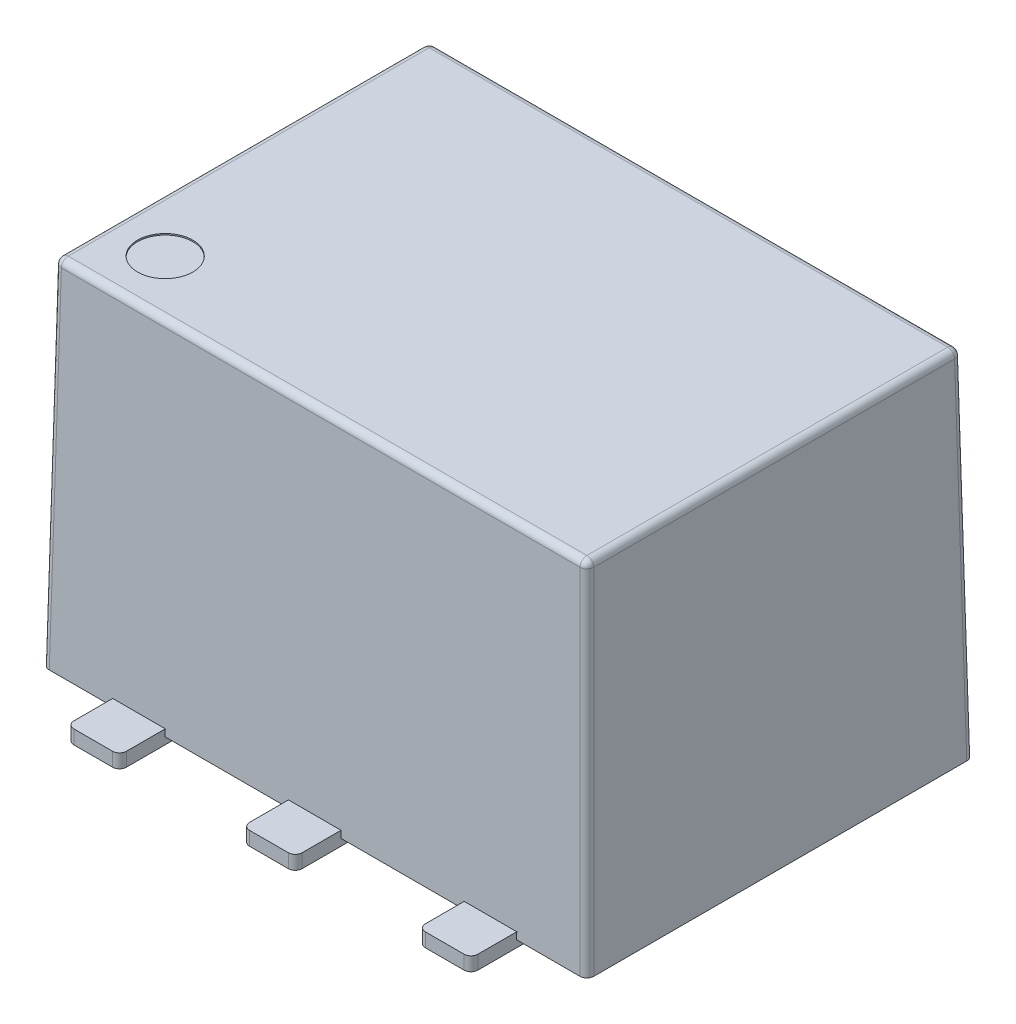
SolidWorks part; units mm, degrees
ref_plane "Спереди" through (0, 0, 0) normal (0, 0, 1) x (1, 0, 0)
ref_plane "Сверху" through (0, 0, 0) normal (0, 1, 0) x (1, 0, 0)
ref_plane "Справа" through (0, 0, 0) normal (1, 0, 0) x (0, 0, -1)
other "Configuration Table"
sketch "Sketch1" plane through (0, 0, 0) normal (0, 1, 0) x (1, 0, 0)
  line L1 (-3.935, 2.795) -> (3.935, 2.795)
  line L2 (-3.935, 2.795) -> (-3.935, -2.795)
  line L3 (-3.935, -2.795) -> (3.935, -2.795)
  line L4 (3.935, 2.795) -> (3.935, -2.795)
  line L5 (-3.935, 2.795) -> (3.935, -2.795) construction
  line L6 (-3.935, -2.795) -> (3.935, 2.795) construction
  point P0 (0, 0)
  dimension "D1" = 5.59
  dimension "D2" = 7.87
extrude "Boss-Extrude1" add sketch "Sketch1" along normal blind 5.13 draft 1
sketch "Sketch2" plane through (0, 0, 0) normal (0, -1, 0) x (1, 0, 0)
  line L0 (0, 0) -> (0, 2.295) construction
  line L1 (-0.38, 3.455) -> (0.38, 3.455)
  line L2 (-0.38, 3.455) -> (-0.38, 2.295)
  line L3 (-0.38, 2.295) -> (0.38, 2.295)
  line L4 (0.38, 3.455) -> (0.38, 2.295)
  line L5 (-3.935, 2.795) -> (3.935, 2.795) construction
  line L6 (2.92, 2.295) -> (2.16, 2.295)
  line L7 (-2.92, 3.455) -> (-2.16, 3.455)
  line L8 (-2.92, 3.455) -> (-2.92, 2.295)
  line L9 (-2.92, 2.295) -> (-2.16, 2.295)
  line L10 (-2.16, 3.455) -> (-2.16, 2.295)
  line L11 (2.16, 3.455) -> (2.16, 2.295)
  line L12 (2.92, 3.455) -> (2.16, 3.455)
  line L13 (2.92, 3.455) -> (2.92, 2.295)
  line L14 (0, 0) -> (3.935, 0) construction
  line L15 (3.935, 2.795) -> (3.935, -2.795) construction
  line L16 (-2.92, -2.295) -> (-2.16, -2.295)
  line L17 (-2.16, -3.455) -> (-2.16, -2.295)
  line L18 (-2.92, -3.455) -> (-2.16, -3.455)
  line L19 (-2.92, -3.455) -> (-2.92, -2.295)
  line L20 (-0.38, -2.295) -> (0.38, -2.295)
  line L21 (0.38, -3.455) -> (0.38, -2.295)
  line L22 (-0.38, -3.455) -> (0.38, -3.455)
  line L23 (-0.38, -3.455) -> (-0.38, -2.295)
  line L24 (2.92, -3.455) -> (2.92, -2.295)
  line L25 (2.92, -3.455) -> (2.16, -3.455)
  line L26 (2.16, -3.455) -> (2.16, -2.295)
  line L27 (2.92, -2.295) -> (2.16, -2.295)
  dimension "D1" = 0.76
  dimension "D2" = 3.455
  dimension "D3" = 0.5
  dimension "D4" = 2.54
extrude "Boss-Extrude2" add sketch "Sketch2" along normal mid plane 0.2
fillet "Fillet1" radius 0.1 20 edges at (0, 5.13, 2.7055) (-3.8455, 5.13, 0) (0, 5.13, -2.7055) (3.8455, 5.13, 0) (-2.92, 0, -3.455) (-2.16, 0, -3.455) (-0.38, 0, -3.455) (0.38, 0, -3.455) (2.16, 0, -3.455) (2.92, 0, -3.455) (-2.92, 0, 3.455) (-2.16, 0, 3.455) (-0.38, 0, 3.455) (0.38, 0, 3.455) (2.92, 0, 3.455) (2.16, 0, 3.455) (3.8902, 2.565, -2.7502) (-3.8902, 2.565, -2.7502) (3.8902, 2.565, 2.7502) (-3.8902, 2.565, 2.7502)
sketch "Sketch3" plane through (0, 5.13, 0) normal (0, 1, 0) x (1, 0, 0)
  line L0 (-3.7472, -2.6072) -> (3.7472, -2.6072) construction
  line L1 (-3.7472, 2.6072) -> (-3.7472, -2.6072) construction
  circle A0 centre (-3.0472, -1.9072) radius 0.4
  dimension "D3" = 0.8
  dimension "D1" = 0.7
  dimension "D2" = 0.7
extrude "Cut-Extrude1" cut sketch "Sketch3" against normal blind 0.02
